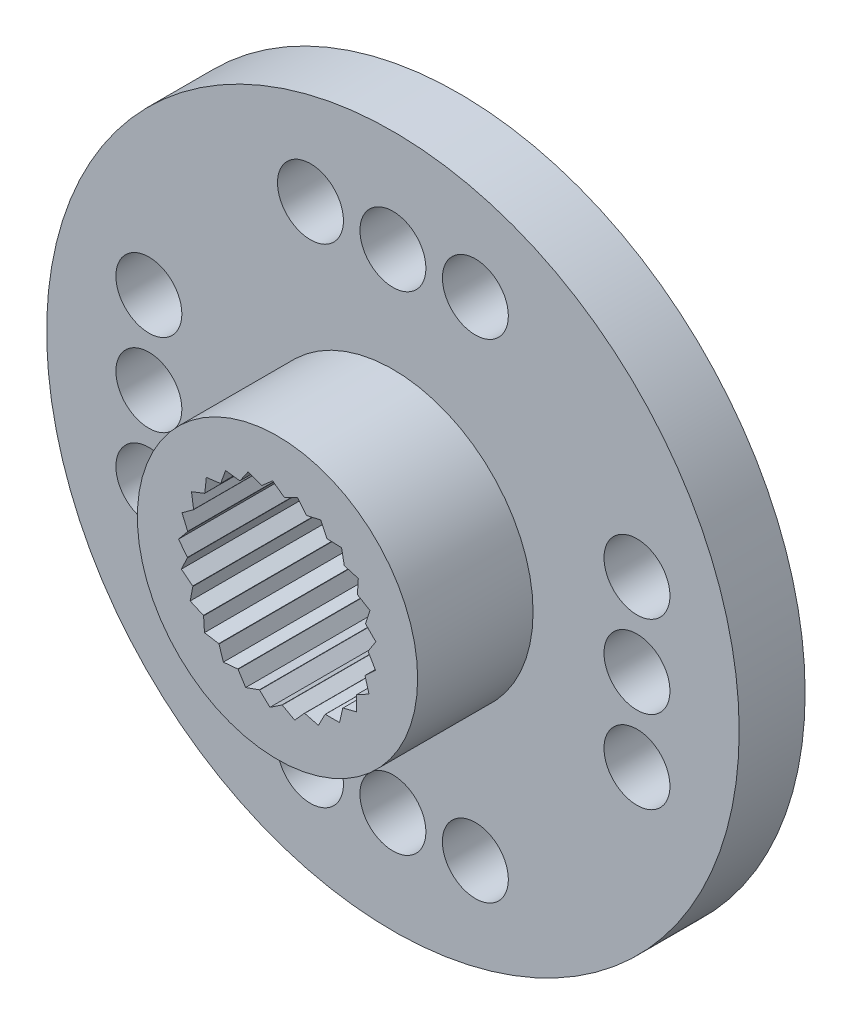
SolidWorks part; units mm, degrees
ref_plane "Front Plane" through (0, 0, 0) normal (0, 0, 1) x (1, 0, 0)
ref_plane "Top Plane" through (0, 0, 0) normal (0, 1, 0) x (1, 0, 0)
ref_plane "Right Plane" through (0, 0, 0) normal (1, 0, 0) x (0, 0, -1)
sketch "Sketch1" plane through (0, 0, 0) normal (0, 0, 1) x (1, 0, 0)
  circle A0 centre (0, 0) radius 10.5
  dimension "D1" = 21
extrude "Boss-Extrude1" add sketch "Sketch1" along normal blind 2
sketch "Sketch2" plane through (0, 0, 2) normal (0, 0, 1) x (1, 0, 0)
  circle A0 centre (0, 0) radius 4.25
  dimension "D1" = 8.5
extrude "Boss-Extrude2" add sketch "Sketch2" along normal blind 3.5
sketch "Sketch3" plane through (0, 0, 5.5) normal (0, 0, 1) x (1, 0, 0)
  circle A0 centre (0, 0) radius 2.75
  dimension "D1" = 5.5
extrude "Cut-Extrude1" cut sketch "Sketch3" against normal blind 4.5
sketch "Sketch4" plane through (0, 0, 0) normal (0, 0, 1) x (1, 0, 0)
  circle A0 centre (0, 0) radius 1.6
  dimension "D1" = 3.2
extrude "Cut-Extrude2" cut sketch "Sketch4" along normal blind 3.5
sketch "Sketch5" plane through (0, 0, 2) normal (0, 0, 1) x (1, 0, 0)
  line L0 (-10.5, 0) -> (10.5, 0) construction
  line L1 (-2.5, 7.4) -> (0, 7.4) construction
  line L2 (0, 7.4) -> (2.5, 7.4) construction
  line L3 (0, 7.4) -> (0, 0) construction
  line L4 (0, -7.4) -> (2.5, -7.4) construction
  line L5 (-2.5, -7.4) -> (0, -7.4) construction
  line L6 (7.4, 2.5) -> (7.4, 0) construction
  line L7 (7.4, 0) -> (7.4, -2.5) construction
  line L8 (-7.4, 0) -> (-7.4, -2.5) construction
  line L9 (-7.4, 2.5) -> (-7.4, 0) construction
  circle A0 centre (0, 7.4) radius 1
  circle A1 centre (-2.5, 7.4) radius 1
  circle A2 centre (2.5, 7.4) radius 1
  circle A3 centre (0, 0) radius 10.5 construction
  circle A4 centre (2.5, -7.4) radius 1
  circle A5 centre (-2.5, -7.4) radius 1
  circle A6 centre (0, -7.4) radius 1
  circle A7 centre (7.4, 0) radius 1
  circle A8 centre (7.4, 2.5) radius 1
  circle A9 centre (7.4, -2.5) radius 1
  circle A10 centre (-7.4, -2.5) radius 1
  circle A11 centre (-7.4, 2.5) radius 1
  circle A12 centre (-7.4, 0) radius 1
  dimension "D1" = 2
  dimension "D2" = 2
  dimension "D3" = 2
  dimension "D7" = 2
  dimension "D8" = 2
  dimension "D9" = 2
  dimension "D4" = 2.5
  dimension "D5" = 2.5
  dimension "D6" = 7.4
  dimension "D10" = 2.5
  dimension "D11" = 2.5
  dimension "D12" = 7.4
extrude "Cut-Extrude3" cut sketch "Sketch5" against normal blind 3.5
sketch "Sketch6" plane through (0, 0, 5.5) normal (0, 0, 1) x (1, 0, 0)
  line L0 (-0.9385, 2.5849) -> (-1.5278, 2.371)
  line L1 (0, 0) -> (-2.971, 0.4161)
  line L2 (0, 0) -> (-2.8954, 0.7852)
  line L3 (-2.8954, 0.7852) -> (-2.7234, 0.3814)
  line L4 (-2.8954, 0.7852) -> (-2.5466, 1.0378)
  line L5 (0, 0) -> (-2.7782, 1.1322)
  circle A0 centre (0, 0) radius 2.75
  circle A1 centre (0, 0) radius 2.75 construction
  circle A2 centre (0, 0) radius 3
  circle M4 centre (0, 0) radius 2.75
  dimension "D3" = 6
  dimension "D1" = 7.2
  dimension "D2" = 14.2
extrude "Cut-Extrude4" cut sketch "Sketch6" against normal blind 4.5 contours L4 L2 M4 | L2 L3 M4
pattern_circular "CirPattern1" count 25 over 360 about axis through (0, 0, 0) along (0, 0, 1) of "Cut-Extrude4"
